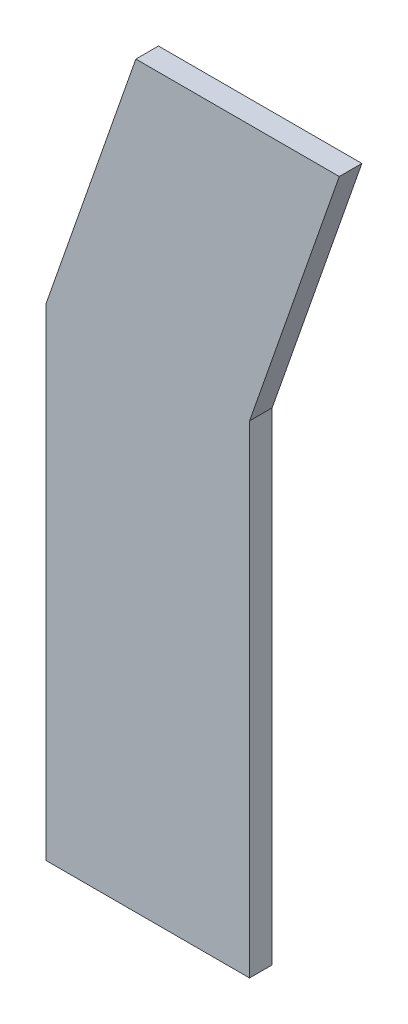
SolidWorks part; units mm, degrees
ref_plane "Front" through (0, 0, 0) normal (0, 0, 1) x (1, 0, 0)
ref_plane "Top" through (0, 0, 0) normal (0, 1, 0) x (1, 0, 0)
ref_plane "Right" through (0, 0, 0) normal (1, 0, 0) x (0, 0, -1)
sketch "Sketch1" plane through (0, 0, 0) normal (0, 0, 1) x (1, 0, 0)
  line L2 (0, 0) -> (0, -426.89)
  line L3 (0, -426.89) -> (180, -426.89)
  line L4 (180, -426.89) -> (180, 0)
  line L8 (259.3989, 226.9815) -> (79.3989, 226.9815)
  line L9 (0, 0) -> (79.3989, 226.9815)
  line L10 (180, 0) -> (259.3989, 226.9815)
  point P3 (0, 0)
  point P7 (259.0414, 226.9815)
  dimension "D1" = 160.72
  dimension "D2" = 180
  dimension "D3" = 426.89
  dimension "D4" = 226.9815
  dimension "D5" = 180
  dimension "D7" = 160.72
extrude "Boss-Extrude1" add sketch "Sketch1" along normal blind 20
